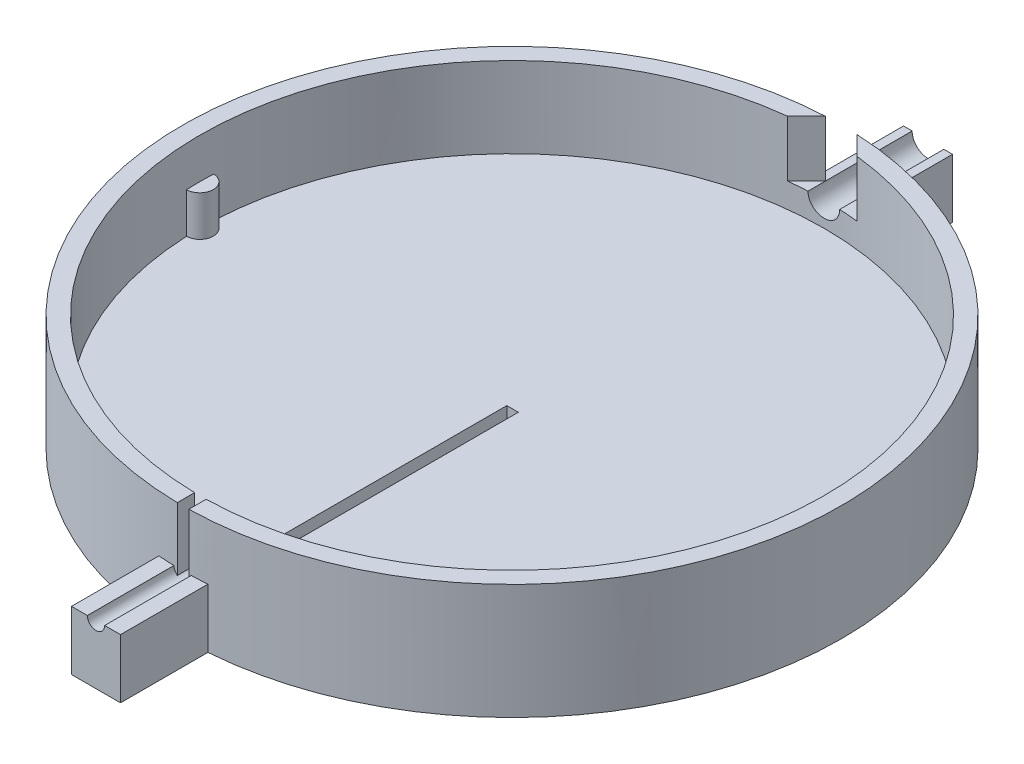
SolidWorks part; units mm, degrees
ref_plane "Front Plane" through (0, 0, 0) normal (0, 0, 1) x (1, 0, 0)
ref_plane "Top Plane" through (0, 0, 0) normal (0, 1, 0) x (1, 0, 0)
ref_plane "Right Plane" through (0, 0, 0) normal (1, 0, 0) x (0, 0, -1)
sketch "Sketch1" plane through (0, 0, 0) normal (0, 1, 0) x (1, 0, 0)
  circle A0 centre (0, 0) radius 57.15
  dimension "D1" = 114.3
extrude "Boss-Extrude1" add sketch "Sketch1" along normal blind 20
sketch "Sketch2" plane through (0, 20, 0) normal (0, 1, 0) x (1, 0, 0)
  circle A0 centre (0, 0) radius 54.15
  circle A1 centre (0, 0) radius 57.15 construction
  circle A2 centre (0, 0) radius 57.15
  dimension "D1" = 3
extrude "Cut-Extrude1" cut sketch "Sketch2" against normal blind 14 contours A0
sketch "Sketch3" plane through (0, 6, 0) normal (0, 1, 0) x (1, 0, 0)
  arc A0 (-54.099, -2.3494) -> (-54.099, 2.3494) centre (-54.15, 0) ccw
  circle A1 centre (0, 0) radius 54.15 construction
  arc A2 (54.099, 2.3494) -> (54.099, -2.3494) centre (54.15, 0) ccw
  arc A3 (54.099, -2.3494) -> (54.099, 2.3494) centre (0, 0) ccw
  arc A4 (-54.099, 2.3494) -> (-54.099, -2.3494) centre (0, 0) ccw
  dimension "D1" = 4.7
  dimension "D2" = 4.7
extrude "Boss-Extrude2" add sketch "Sketch3" along normal blind 7
sketch "Sketch4" plane through (0, 0, 0) normal (0, 0, 1) x (1, 0, 0)
  line L0 (54.099, 6) -> (-54.099, 6) construction
  line L1 (54.099, 6) -> (-54.099, 6)
  line L2 (0, 0) -> (0, 4.7714)
  line L3 (54.15, 20) -> (-54.15, 20) construction
  line L4 (54.15, 20) -> (-54.15, 20)
  line L5 (-2.75, 10.25) -> (-2.75, 20)
  line L6 (2.75, 10.25) -> (2.75, 20)
  circle A0 centre (0, 10.25) radius 2.75
  dimension "D1" = 5.5
  dimension "D2" = 4.25
extrude "Cut-Extrude2" cut sketch "Sketch4" against normal through all contours A0 L6 L4 L5
sketch "Sketch5" plane through (0, 0, 0) normal (0, 0, 1) x (1, 0, 0)
  line L0 (54.15, 20) -> (-54.15, 20) construction
  line L1 (1.0982, 3.999) -> (-0.9018, 3.999)
  line L2 (1.0982, 3.999) -> (1.0982, 20)
  line L3 (1.0982, 5.999) -> (-0.9018, 5.999)
  line L4 (-0.9018, 3.999) -> (-0.9018, 20)
  line L5 (1.0982, 3.999) -> (-0.9018, 5.999) construction
  line L6 (1.0982, 5.999) -> (-0.9018, 3.999) construction
  line L7 (1.0982, 20) -> (-0.9018, 20)
  point P0 (0.0982, 4.999)
  dimension "D1" = 2
  dimension "D2" = 2
  dimension "D3" = 5
extrude "Cut-Extrude3" cut sketch "Sketch5" along normal through all contours L2 L7 L4 L1
ref_plane "Plane1" through (0, 0, -54.15) normal (0, 0, 1) x (1, 0, 0)
sketch "Sketch6" plane through (0, 0, -54.15) normal (0, 0, 1) x (1, 0, 0)
  line L0 (-57.15, 0) -> (57.15, 0) construction
  line L1 (-4.25, 0) -> (4.25, 0)
  line L2 (4.25, 10.25) -> (4.25, 0)
  line L3 (-4.25, 10.25) -> (-4.25, 0)
  line L4 (-4.25, 10.25) -> (-2.75, 10.25)
  line L5 (-2.75, 10.25) -> (-2.7454, 6.232)
  line L6 (2.75, 10.25) -> (4.25, 10.25)
  arc A0 (-2.75, 10.25) -> (2.75, 10.25) centre (0, 10.25) ccw construction
  arc A1 (-2.75, 10.25) -> (2.75, 10.25) centre (0, 10.25) ccw
extrude "Boss-Extrude3" add sketch "Sketch6" against normal blind 18 contours A1 L6 L2 L1 L3 L4
ref_plane "Plane2" through (0, 0, 54.15) normal (0, 0, -1) x (-1, 0, 0)
sketch "Sketch7" plane through (0, 0, 54.15) normal (0, 0, -1) x (-1, 0, 0)
  line L5 (4.25, 10.25) -> (2.75, 10.25)
  line L6 (-2.75, 10.25) -> (-4.25, 10.25)
  line L7 (-4.25, 10.25) -> (-4.25, 0)
  line L8 (-4.25, 0) -> (4.25, 0)
  line L9 (4.25, 0) -> (4.25, 10.25)
  line L10 (4.25, 10.25) -> (1.5, 10.25)
  line L11 (-1.5, 10.25) -> (-4.25, 10.25)
  line L12 (-4.25, 10.25) -> (-4.25, 0)
  line L13 (-4.25, 0) -> (4.25, 0)
  line L14 (4.25, 0) -> (4.25, 10.25)
  arc A0 (-1.5, 10.25) -> (1.5, 10.25) centre (0, 10.25) ccw
  arc A1 (-2.75, 10.25) -> (2.75, 10.25) centre (0, 10.25) ccw
  dimension "D2" = 3
  dimension "D1" = 0
extrude "Boss-Extrude4" add sketch "Sketch7" against normal blind 18
sketch "Sketch8" plane through (0, 20, 0) normal (0, 1, 0) x (1, 0, 0)
  line L0 (2.75, 54.0801) -> (2.75, 57.0838) construction
  line L1 (-2.75, 54.0801) -> (-2.75, 57.0838) construction
  line L2 (2.75, 54.0801) -> (2.75, 57.0838)
  line L3 (-2.75, 54.0801) -> (-2.75, 57.0838)
  line L4 (-2.75, 57.0838) -> (-6.0194, 53.8144)
  line L5 (2.75, 57.0838) -> (6.0194, 53.8144)
  arc A0 (-2.75, 54.0801) -> (-0.9018, -54.1425) centre (0, 0) ccw construction
  arc A1 (1.0982, -54.1389) -> (2.75, 54.0801) centre (0, 0) ccw construction
  arc A2 (-2.75, 54.0801) -> (-6.0194, 53.8144) centre (0, 0) ccw
  arc A3 (6.0194, 53.8144) -> (2.75, 54.0801) centre (0, 0) ccw
  dimension "D1" = 45
  dimension "D2" = 45
extrude "Cut-Extrude4" cut sketch "Sketch8" against normal up to surface (9.75 mm away) up to face at (3.5001, 10.25, -64.5951)
